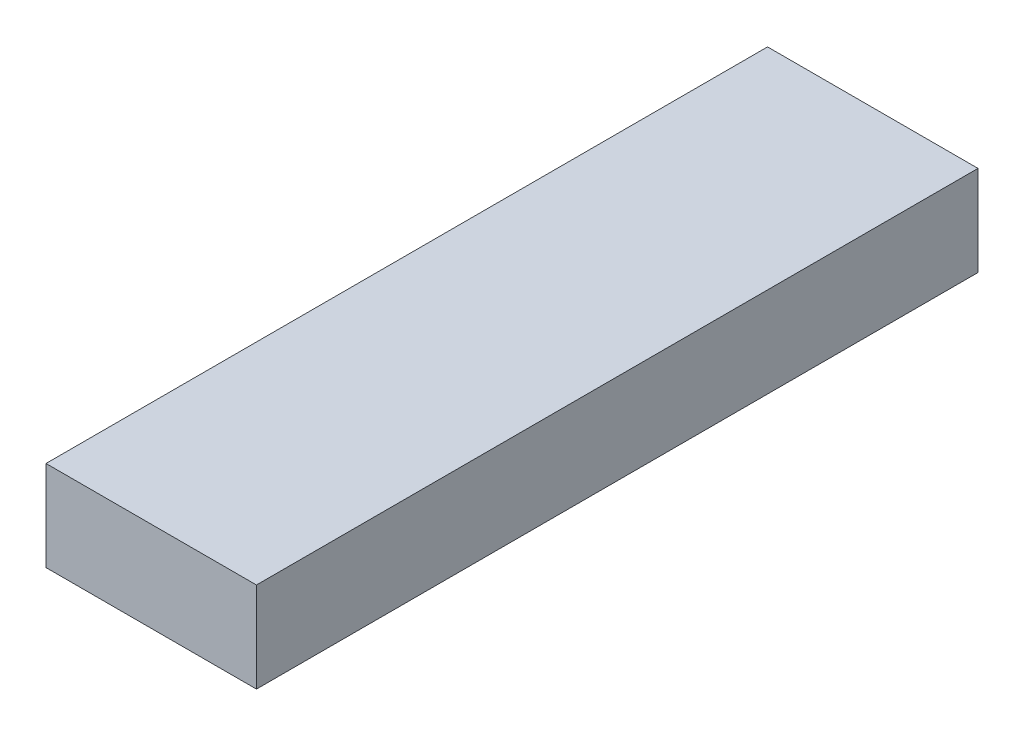
SolidWorks part; units mm, degrees
material "Pine"
ref_plane "Front Plane" through (0, 0, 0) normal (0, 0, 1) x (1, 0, 0)
ref_plane "Top Plane" through (0, 0, 0) normal (0, 1, 0) x (1, 0, 0)
ref_plane "Right Plane" through (0, 0, 0) normal (1, 0, 0) x (0, 0, -1)
sketch "Sketch1" plane through (0, 0, 0) normal (0, 0, 1) x (1, 0, 0)
  line L1 (0, 0) -> (88.9, 0)
  line L2 (0, 0) -> (0, 38.1)
  line L3 (0, 38.1) -> (88.9, 38.1)
  line L4 (88.9, 0) -> (88.9, 38.1)
  dimension "D1" = 88.9
  dimension "D2" = 38.1
extrude "Boss-Extrude1" add sketch "Sketch1" along normal blind 304.8
